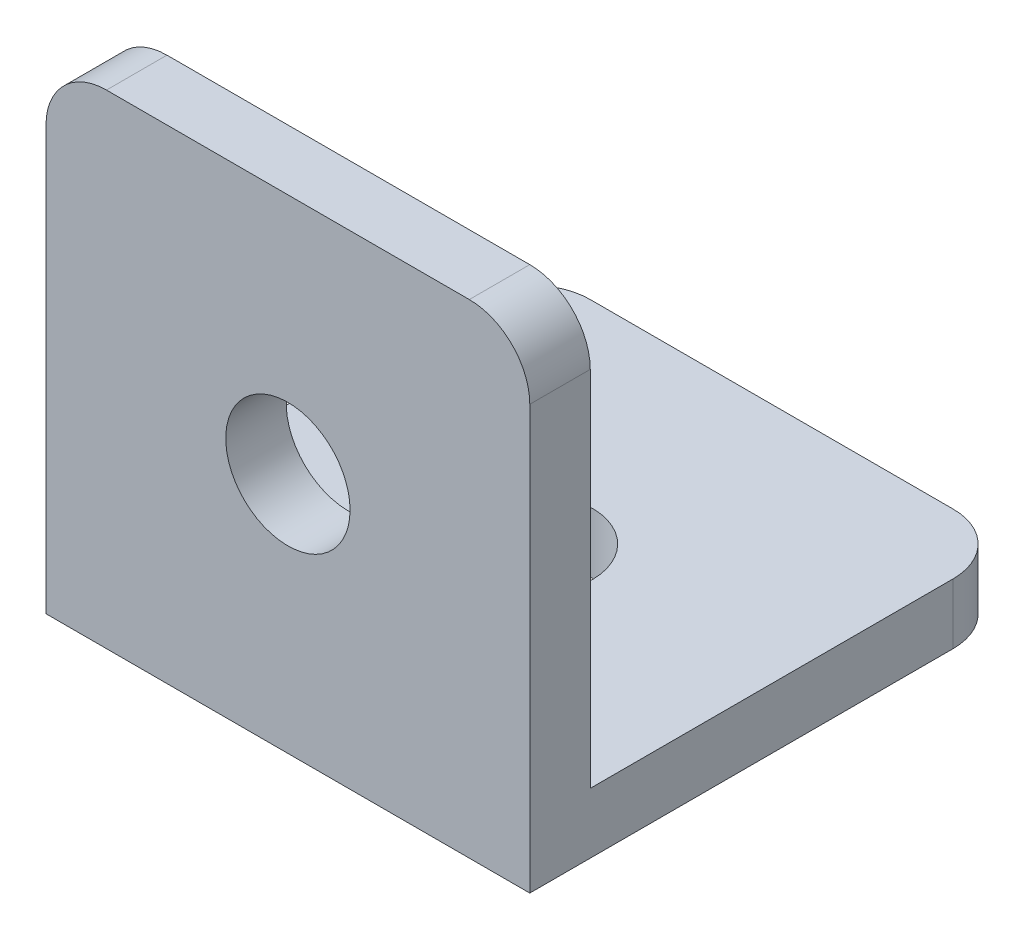
SolidWorks part; units mm, degrees
material "3003 Alloy"
ref_plane "Front Plane" through (0, 0, 0) normal (0, 0, 1) x (1, 0, 0)
ref_plane "Top Plane" through (0, 0, 0) normal (0, 1, 0) x (1, 0, 0)
ref_plane "Right Plane" through (0, 0, 0) normal (1, 0, 0) x (0, 0, -1)
sketch "Sketch1" plane through (0, 0, 0) normal (0, 1, 0) x (1, 0, 0)
  line L0 (12.7, 0) -> (12.7, 25.4) construction
  line L1 (0, 0) -> (25.4, 0)
  line L2 (0, 0) -> (0, 25.4)
  line L3 (0, 25.4) -> (25.4, 25.4)
  line L4 (25.4, 0) -> (25.4, 25.4)
  circle A0 centre (12.7, 12.7) radius 3.2639
  dimension "D3" = 6.5278
  dimension "D1" = 25.4
  dimension "D2" = 25.4
extrude "Boss-Extrude1" add sketch "Sketch1" along normal blind 3.175
sketch "Sketch2" plane through (0, 3.175, 0) normal (0, 1, 0) x (1, 0, 0)
  line L0 (25.4, 0) -> (25.4, 25.4) construction
  line L1 (0, 0) -> (25.4, 0)
  line L2 (0, 0) -> (0, 3.175)
  line L3 (0, 3.175) -> (25.4, 3.175)
  line L4 (25.4, 0) -> (25.4, 3.175)
  dimension "D1" = 3.175
extrude "Boss-Extrude2" add sketch "Sketch2" along normal blind 22.225
sketch "Sketch3" plane through (0, 0, 0) normal (0, 0, 1) x (1, 0, 0)
  line L0 (12.7, 0) -> (12.7, 25.4) construction
  line L1 (0, 0) -> (25.4, 0) construction
  line L2 (0, 25.4) -> (25.4, 25.4) construction
  circle A0 centre (12.7, 12.7) radius 3.2639
  dimension "D1" = 6.5278
extrude "Cut-Extrude1" cut sketch "Sketch3" against normal blind 3.175
fillet "Fillet1" radius 3.175 4 edges at (25.4, 1.5875, -25.4) (0, 1.5875, -25.4) (0, 25.4, -1.5875) (25.4, 25.4, -1.5875)
